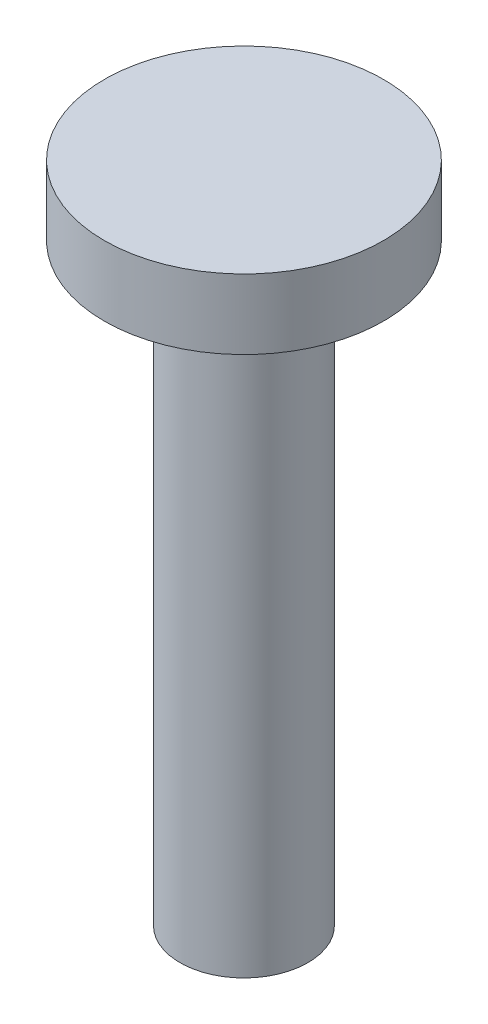
SolidWorks part; units mm, degrees
ref_plane "Front" through (0, 0, 0) normal (0, 0, 1) x (1, 0, 0)
ref_plane "Top" through (0, 0, 0) normal (0, 1, 0) x (1, 0, 0)
ref_plane "Right" through (0, 0, 0) normal (1, 0, 0) x (0, 0, -1)
sketch "Sketch1" plane through (0, 0, 0) normal (0, 1, 0) x (1, 0, 0)
  circle A0 centre (0, 0) radius 10
  dimension "D1" = 20
extrude "Boss-Extrude1" add sketch "Sketch1" along normal blind 85
scale "축척1" scale about centroid uniform scaling yes scale factor 0.3
sketch "스케치1" plane through (0, 55.25, 0) normal (0, 1, 0) x (1, 0, 0)
  circle A0 centre (0, 0) radius 6
  dimension "D1" = 12
extrude "보스-돌출1" add sketch "스케치1" along normal blind 3
sketch "스케치2" plane through (0, 29.75, 0) normal (0, -1, 0) x (1, 0, 0)
  circle A0 centre (0, 0) radius 3
  circle A1 centre (0, 0) radius 2.75
  dimension "D1" = 6
  dimension "D2" = 0.25
extrude "컷-돌출1" cut sketch "스케치2" against normal up to surface (25.5 mm away) up to face at (0, 55.25, 3)
